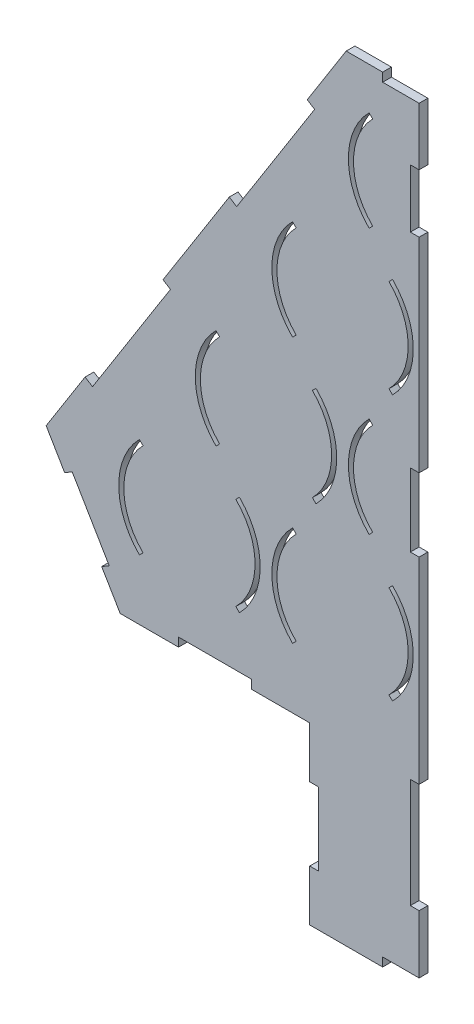
SolidWorks part; units mm, degrees
ref_plane "Plan de face" through (0, 0, 0) normal (0, 0, 1) x (1, 0, 0)
ref_plane "Plan de dessus" through (0, 0, 0) normal (0, 1, 0) x (1, 0, 0)
ref_plane "Plan de droite" through (0, 0, 0) normal (1, 0, 0) x (0, 0, -1)
sketch "Esquisse1" plane through (0, 0, 0) normal (0, 0, 1) x (1, 0, 0)
  line L0 (0, 0) -> (-371.1464, 0) construction
  line L1 (0, 0) -> (478.5179, 0) construction
  line L2 (0, 0) -> (0, 90.9327) construction
  line L3 (0, 90.9327) -> (-157.5, 90.9327) construction
  line L4 (0, 90.9327) -> (157.5, 90.9327) construction
  line L5 (0, 90.9327) -> (0, 181.8653) construction
  line L6 (0, 181.8653) -> (-52.5, 181.8653) construction
  line L7 (0, 181.8653) -> (52.5, 181.8653) construction
  line L8 (0, 181.8653) -> (0, 363.4062) construction
  line L12 (-157.5, 0) -> (-189.3198, -31.8198) construction
  line L13 (-157.5, 0) -> (-189.3198, 31.8198) construction
  line L14 (-189.3198, 31.8198) -> (-191.7947, 34.2947)
  line L15 (-189.3198, -31.8198) -> (-191.7947, -34.2947)
  line L16 (-157.5, 0) -> (-157.5, 43.1504) construction
  line L17 (-125.6802, 31.8198) -> (-123.2053, 34.2947)
  line L18 (-125.6802, -31.8198) -> (-123.2053, -34.2947)
  line L19 (-84.3198, -31.8198) -> (-86.7947, -34.2947)
  line L20 (-84.3198, 31.8198) -> (-86.7947, 34.2947)
  line L21 (-20.6802, 31.8198) -> (-18.2053, 34.2947)
  line L22 (-20.6802, -31.8198) -> (-18.2053, -34.2947)
  line L23 (20.6802, -31.8198) -> (18.2053, -34.2947)
  line L24 (20.6802, 31.8198) -> (18.2053, 34.2947)
  line L25 (84.3198, 31.8198) -> (86.7947, 34.2947)
  line L26 (84.3198, -31.8198) -> (86.7947, -34.2947)
  line L27 (125.6802, -31.8198) -> (123.2053, -34.2947)
  line L28 (125.6802, 31.8198) -> (123.2053, 34.2947)
  line L29 (189.3198, 31.8198) -> (191.7947, 34.2947)
  line L30 (189.3198, -31.8198) -> (191.7947, -34.2947)
  line L31 (-105, 90.9327) -> (-136.8198, 122.7525) construction
  line L32 (-105, 90.9327) -> (-136.8198, 59.1129) construction
  line L33 (-139.2947, 56.638) -> (-136.8198, 59.1129)
  line L34 (-136.8198, 122.7525) -> (-139.2947, 125.2273)
  line L35 (-105, 90.9327) -> (-105, 127.4436) construction
  line L36 (-70.7053, 56.638) -> (-73.1802, 59.1129)
  line L37 (-73.1802, 122.7525) -> (-70.7053, 125.2273)
  line L38 (-31.8198, 122.7525) -> (-34.2947, 125.2273)
  line L39 (-34.2947, 56.638) -> (-31.8198, 59.1129)
  line L40 (34.2947, 56.638) -> (31.8198, 59.1129)
  line L41 (31.8198, 122.7525) -> (34.2947, 125.2273)
  line L42 (73.1802, 122.7525) -> (70.7053, 125.2273)
  line L43 (70.7053, 56.638) -> (73.1802, 59.1129)
  line L44 (139.2947, 56.638) -> (136.8198, 59.1129)
  line L45 (136.8198, 122.7525) -> (139.2947, 125.2273)
  line L46 (-52.5, 181.8653) -> (-86.7947, 216.16) construction
  line L47 (-52.5, 181.8653) -> (-86.7947, 147.5707) construction
  line L48 (-52.5, 181.8653) -> (-100, 181.8653) construction
  line L49 (-84.3198, 213.6851) -> (-86.7947, 216.16)
  line L50 (-84.3198, 150.0455) -> (-86.7947, 147.5707)
  line L51 (-52.5, 181.8653) -> (-52.5, 219.5882) construction
  line L52 (-20.6802, 213.6851) -> (-18.2053, 216.16)
  line L53 (-20.6802, 150.0455) -> (-18.2053, 147.5707)
  line L54 (20.6802, 150.0455) -> (18.2053, 147.5707)
  line L55 (20.6802, 213.6851) -> (18.2053, 216.16)
  line L56 (84.3198, 150.0455) -> (86.7947, 147.5707)
  line L57 (84.3198, 213.6851) -> (86.7947, 216.16)
  line L58 (0, 272.798) -> (-34.2947, 307.0927) construction
  line L59 (0, 272.798) -> (-47.5, 272.798) construction
  line L60 (0, 272.798) -> (-34.2947, 238.5033) construction
  line L61 (-31.8198, 304.6178) -> (-34.2947, 307.0927)
  line L62 (-31.8198, 240.9782) -> (-34.2947, 238.5033)
  line L63 (31.8198, 304.6178) -> (34.2947, 307.0927)
  line L64 (31.8198, 240.9782) -> (34.2947, 238.5033)
  line L65 (-50, 335.9011) -> (50, 335.9011)
  line L66 (-255.7759, 10.5071) -> (-205, -75.6429)
  line L67 (255.7759, 10.5071) -> (205, -75.6429)
  line L68 (-205, -75.6429) -> (205, -75.6429)
  line L69 (-50, 335.9011) -> (-255.7759, 10.5071)
  line L70 (50, 335.9011) -> (255.7759, 10.5071)
  line L71 (50, 335.9011) -> (50, -75.6429) construction
  line L72 (-50, 335.9011) -> (-50, -75.6429) construction
  arc A10 (-189.3198, -31.8198) -> (-189.3198, 31.8198) centre (-157.5, 0) cw
  arc A11 (-191.7947, -34.2947) -> (-191.7947, 34.2947) centre (-157.5, 0) cw
  arc A12 (-125.6802, -31.8198) -> (-125.6802, 31.8198) centre (-157.5, 0) ccw
  arc A13 (-123.2053, -34.2947) -> (-123.2053, 34.2947) centre (-157.5, 0) ccw
  arc A14 (-86.7947, -34.2947) -> (-86.7947, 34.2947) centre (-52.5, 0) cw
  arc A15 (-84.3198, -31.8198) -> (-84.3198, 31.8198) centre (-52.5, 0) cw
  arc A16 (-20.6802, -31.8198) -> (-20.6802, 31.8198) centre (-52.5, 0) ccw
  arc A17 (-18.2053, -34.2947) -> (-18.2053, 34.2947) centre (-52.5, 0) ccw
  arc A18 (18.2053, -34.2947) -> (18.2053, 34.2947) centre (52.5, 0) cw
  arc A19 (20.6802, -31.8198) -> (20.6802, 31.8198) centre (52.5, 0) cw
  arc A20 (84.3198, -31.8198) -> (84.3198, 31.8198) centre (52.5, 0) ccw
  arc A21 (86.7947, -34.2947) -> (86.7947, 34.2947) centre (52.5, 0) ccw
  arc A22 (123.2053, -34.2947) -> (123.2053, 34.2947) centre (157.5, 0) cw
  arc A23 (125.6802, -31.8198) -> (125.6802, 31.8198) centre (157.5, 0) cw
  arc A24 (189.3198, -31.8198) -> (189.3198, 31.8198) centre (157.5, 0) ccw
  arc A25 (191.7947, -34.2947) -> (191.7947, 34.2947) centre (157.5, 0) ccw
  arc A26 (-136.8198, 122.7525) -> (-136.8198, 59.1129) centre (-105, 90.9327) ccw
  arc A27 (-139.2947, 125.2273) -> (-139.2947, 56.638) centre (-105, 90.9327) ccw
  arc A28 (-73.1802, 122.7525) -> (-73.1802, 59.1129) centre (-105, 90.9327) cw
  arc A29 (-70.7053, 125.2273) -> (-70.7053, 56.638) centre (-105, 90.9327) cw
  arc A30 (-34.2947, 125.2273) -> (-34.2947, 56.638) centre (0, 90.9327) ccw
  arc A31 (-31.8198, 122.7525) -> (-31.8198, 59.1129) centre (0, 90.9327) ccw
  arc A32 (31.8198, 122.7525) -> (31.8198, 59.1129) centre (0, 90.9327) cw
  arc A33 (34.2947, 125.2273) -> (34.2947, 56.638) centre (0, 90.9327) cw
  arc A34 (70.7053, 125.2273) -> (70.7053, 56.638) centre (105, 90.9327) ccw
  arc A35 (73.1802, 122.7525) -> (73.1802, 59.1129) centre (105, 90.9327) ccw
  arc A36 (136.8198, 122.7525) -> (136.8198, 59.1129) centre (105, 90.9327) cw
  arc A37 (139.2947, 125.2273) -> (139.2947, 56.638) centre (105, 90.9327) cw
  arc A38 (-86.7947, 216.16) -> (-86.7947, 147.5707) centre (-52.5, 181.8653) ccw
  arc A39 (-84.3198, 213.6851) -> (-84.3198, 150.0455) centre (-52.5, 181.8653) ccw
  arc A40 (-20.6802, 213.6851) -> (-20.6802, 150.0455) centre (-52.5, 181.8653) cw
  arc A41 (-18.2053, 216.16) -> (-18.2053, 147.5707) centre (-52.5, 181.8653) cw
  arc A42 (18.2053, 216.16) -> (18.2053, 147.5707) centre (52.5, 181.8653) ccw
  arc A43 (20.6802, 213.6851) -> (20.6802, 150.0455) centre (52.5, 181.8653) ccw
  arc A44 (84.3198, 213.6851) -> (84.3198, 150.0455) centre (52.5, 181.8653) cw
  arc A45 (86.7947, 216.16) -> (86.7947, 147.5707) centre (52.5, 181.8653) cw
  arc A46 (-34.2947, 307.0927) -> (-34.2947, 238.5033) centre (0, 272.798) ccw
  arc A47 (-31.8198, 304.6178) -> (-31.8198, 240.9782) centre (0, 272.798) ccw
  arc A48 (31.8198, 304.6178) -> (31.8198, 240.9782) centre (0, 272.798) cw
  arc A49 (34.2947, 307.0927) -> (34.2947, 238.5033) centre (0, 272.798) cw
  point P7 (-105, 90.9327)
  point P32 (-157.5, 0)
  point P95 (0, 272.798)
  dimension "D4" = 4
  dimension "D5" = 45
  dimension "D6" = 45
  dimension "D7" = 45
  dimension "D8" = 48.5
  dimension "D9" = 3
  dimension "D10" = 45
  dimension "D11" = 45
  dimension "D12" = 45
  dimension "D13" = 48.5
  dimension "D14" = 45
  dimension "D15" = 2
  dimension "D16" = 45
  dimension "D17" = 45
  dimension "D18" = 48.5
  dimension "D19" = 45
  dimension "D20" = 100
  dimension "D21" = 410
  dimension "D27" = 45
  dimension "D30" = 48.5
  dimension "D22" = 32.309
  dimension "D23" = 32.309
  dimension "D24" = 385
  dimension "D25" = 385
  dimension "D26" = 205
  dimension "D28" = 45
  dimension "D29" = 45
  dimension "D31" = 100
  dimension "D32" = 100
extrude "Boss.-Extru.1" add sketch "Esquisse1" along normal blind 6
sketch "Esquisse2" plane through (0, 0, 6) normal (0, 0, 1) x (1, 0, 0)
  line L0 (-205, -75.6429) -> (205, -75.6429) construction
  line L1 (75, -75.6429) -> (-75, -75.6429)
  line L2 (75, -75.6429) -> (75, -195.6429)
  line L3 (75, -195.6429) -> (-75, -195.6429)
  line L4 (-75, -75.6429) -> (-75, -195.6429)
  dimension "D1" = 150
  dimension "D2" = 120
  dimension "D3" = 75
extrude "Boss.-Extru.2" add sketch "Esquisse2" against normal blind 6
sketch "Esquisse3" plane through (0, 0, 6) normal (0, 0, 1) x (1, 0, 0)
  line L0 (-75, -75.6429) -> (-75, -195.6429) construction
  line L1 (-75, -110.6429) -> (-69, -110.6429)
  line L2 (-75, -110.6429) -> (-75, -160.6429)
  line L3 (-75, -160.6429) -> (-69, -160.6429)
  line L4 (-69, -110.6429) -> (-69, -160.6429)
  line L5 (-75, -195.6429) -> (75, -195.6429) construction
  line L6 (-25, -195.6429) -> (25, -195.6429)
  line L7 (-25, -195.6429) -> (-25, -189.6429)
  line L8 (-25, -189.6429) -> (25, -189.6429)
  line L9 (25, -195.6429) -> (25, -189.6429)
  line L10 (75, -195.6429) -> (75, -75.6429) construction
  line L11 (75, -110.6429) -> (69, -110.6429)
  line L12 (75, -110.6429) -> (75, -160.6429)
  line L13 (75, -160.6429) -> (69, -160.6429)
  line L14 (69, -110.6429) -> (69, -160.6429)
  line L15 (-205, -75.6429) -> (-75, -75.6429) construction
  line L16 (75, -75.6429) -> (205, -75.6429) construction
  dimension "D1" = 50
  dimension "D2" = 50
  dimension "D3" = 50
  dimension "D4" = 6
  dimension "D5" = 6
  dimension "D6" = 6
  dimension "D7" = 35
  dimension "D8" = 35
  dimension "D9" = 50
extrude "Enlèv. mat.-Extru.1" cut sketch "Esquisse3" against normal blind 10
sketch "Esquisse4" plane through (0, 0, 6) normal (0, 0, 1) x (1, 0, 0)
  line L0 (-205, -75.6429) -> (-75, -75.6429) construction
  line L1 (-165, -75.6429) -> (-115, -75.6429)
  line L2 (-165, -75.6429) -> (-165, -69.6429)
  line L3 (-165, -69.6429) -> (-115, -69.6429)
  line L4 (-115, -75.6429) -> (-115, -69.6429)
  line L11 (-217.694, -54.1054) -> (-212.525, -51.0588)
  line L12 (-255.7759, 10.5071) -> (-205, -75.6429) construction
  line L13 (-212.525, -51.0588) -> (-237.9129, -7.9839)
  line L14 (-237.9129, -7.9839) -> (-243.0819, -11.0304)
  line L15 (-243.0819, -11.0304) -> (-217.694, -54.1054)
  line L16 (-229.0517, 52.766) -> (-223.9806, 49.5592)
  line L17 (-50, 335.9011) -> (-255.7759, 10.5071) construction
  line L18 (-223.9806, 49.5592) -> (-170.5324, 134.0771)
  line L19 (-170.5324, 134.0771) -> (-175.6034, 137.284)
  line L20 (-175.6034, 137.284) -> (-229.0517, 52.766)
  line L23 (-71.6531, 290.4353) -> (-76.7241, 293.6422)
  line L25 (-71.6531, 290.4353) -> (-125.1013, 205.9173)
  line L26 (-125.1013, 205.9173) -> (-130.1724, 209.1242)
  line L27 (-130.1724, 209.1242) -> (-76.7241, 293.6422)
  line L28 (50, 335.9011) -> (-50, 335.9011) construction
  line L29 (-25, 335.9011) -> (25, 335.9011)
  line L30 (-25, 335.9011) -> (-25, 329.9011)
  line L31 (-25, 329.9011) -> (25, 329.9011)
  line L32 (25, 335.9011) -> (25, 329.9011)
  line L33 (0, 335.9011) -> (0, -65.6429) construction
  line L34 (165, -69.6429) -> (115, -69.6429)
  line L35 (115, -75.6429) -> (115, -69.6429)
  line L36 (165, -75.6429) -> (115, -75.6429)
  line L37 (165, -75.6429) -> (165, -69.6429)
  line L38 (237.9129, -7.9839) -> (243.0819, -11.0304)
  line L39 (212.525, -51.0588) -> (237.9129, -7.9839)
  line L40 (217.694, -54.1054) -> (212.525, -51.0588)
  line L41 (243.0819, -11.0304) -> (217.694, -54.1054)
  line L42 (170.5324, 134.0771) -> (175.6034, 137.284)
  line L43 (223.9806, 49.5592) -> (170.5324, 134.0771)
  line L44 (229.0517, 52.766) -> (223.9806, 49.5592)
  line L45 (175.6034, 137.284) -> (229.0517, 52.766)
  line L46 (125.1013, 205.9173) -> (130.1724, 209.1242)
  line L47 (71.6531, 290.4353) -> (125.1013, 205.9173)
  line L48 (71.6531, 290.4353) -> (76.7241, 293.6422)
  line L49 (130.1724, 209.1242) -> (76.7241, 293.6422)
  dimension "D1" = 6
  dimension "D2" = 50
  dimension "D3" = 6
  dimension "D4" = 50
  dimension "D5" = 40
  dimension "D6" = 25
  dimension "D7" = 6
  dimension "D8" = 100
  dimension "D9" = 6
  dimension "D10" = 50
  dimension "D11" = 50
  dimension "D12" = 100
  dimension "D13" = 6
  dimension "D14" = 50
  dimension "D15" = 25
extrude "Enlèv. mat.-Extru.2" cut sketch "Esquisse4" against normal blind 10
sketch "Esquisse5" plane through (0, 0, 6) normal (0, 0, 1) x (1, 0, 0)
  line L12 (0, 335.9011) -> (0, -195.6429) construction
  line L15 (-255.7759, 10.5071) -> (255.7759, 10.5071) construction
  line L17 (25, -195.6429) -> (75, -195.6429) construction
  line L19 (0, 335.9011) -> (263.3061, 335.9011)
  line L20 (0, 335.9011) -> (0, -195.6429)
  line L21 (0, -195.6429) -> (263.3061, -195.6429)
  line L22 (263.3061, 335.9011) -> (263.3061, -195.6429)
  dimension "D1" = 531.544
  dimension "D3" = 0
extrude "Enlèv. mat.-Extru.5" cut sketch "Esquisse5" against normal blind 10
sketch "Esquisse9" plane through (0, 0, 6) normal (0, 0, 1) x (1, 0, 0)
  line L0 (0, 329.9011) -> (0, -189.6429) construction
  line L1 (0, -149.6429) -> (-6, -149.6429)
  line L2 (0, -149.6429) -> (0, -74.6429)
  line L3 (0, -74.6429) -> (-6, -74.6429)
  line L4 (-6, -149.6429) -> (-6, -74.6429)
  line L5 (0, -189.6429) -> (-25, -189.6429) construction
  line L6 (0, 110.3571) -> (-6, 110.3571)
  line L7 (0, 110.3571) -> (0, 60.3571)
  line L8 (0, 60.3571) -> (-6, 60.3571)
  line L9 (-6, 110.3571) -> (-6, 60.3571)
  line L10 (0, 290.3571) -> (-6, 290.3571)
  line L11 (0, 290.3571) -> (0, 250.3571)
  line L12 (0, 250.3571) -> (-6, 250.3571)
  line L13 (-6, 290.3571) -> (-6, 250.3571)
  dimension "D1" = 6
  dimension "D2" = 6
  dimension "D3" = 6
  dimension "D4" = 50
  dimension "D5" = 75
  dimension "D6" = 40
  dimension "D7" = 135
  dimension "D8" = 140
  dimension "D9" = 40
extrude "Enlèv. mat.-Extru.6" cut sketch "Esquisse9" against normal blind 10
